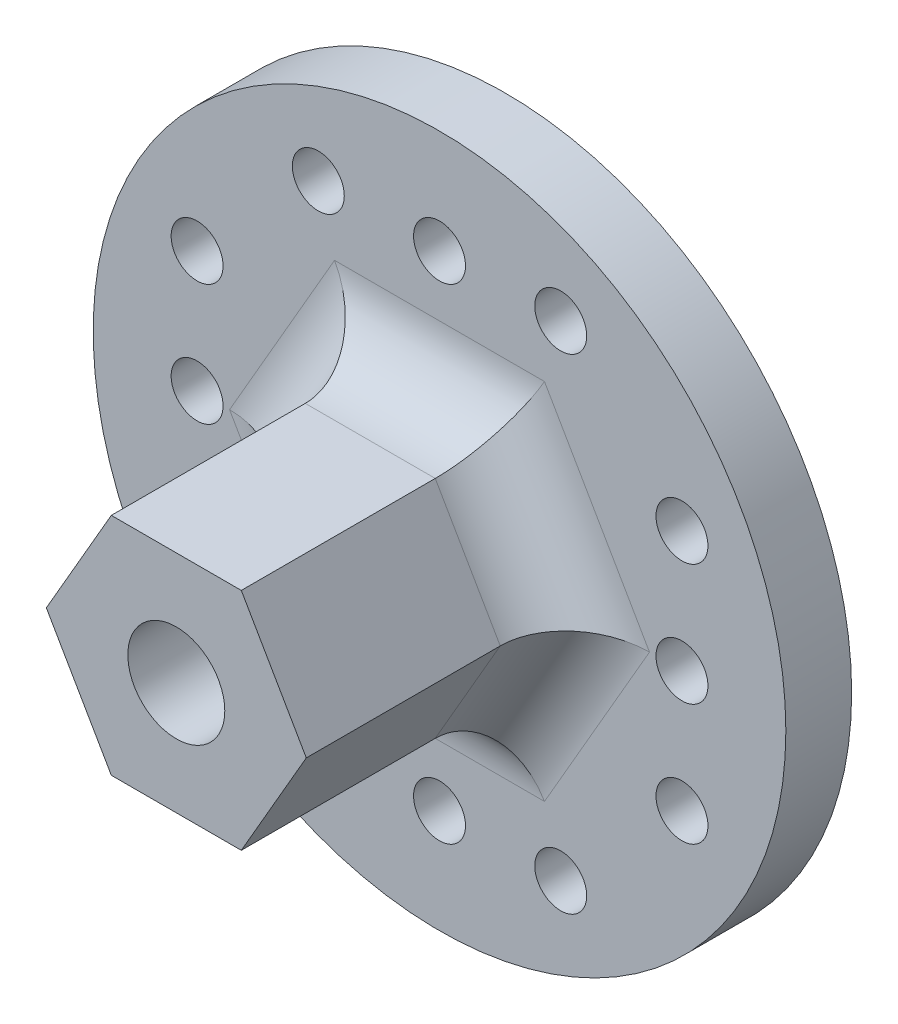
SolidWorks part; units mm, degrees
ref_plane "Front Plane" through (0, 0, 0) normal (0, 0, 1) x (1, 0, 0)
ref_plane "Top Plane" through (0, 0, 0) normal (0, 1, 0) x (1, 0, 0)
ref_plane "Right Plane" through (0, 0, 0) normal (1, 0, 0) x (0, 0, -1)
sketch "Sketch1" plane through (0, 0, 0) normal (0, 0, 1) x (1, 0, 0)
  line L0 (-7, 3.5) -> (-7, -3.5) construction
  line L1 (-7, 0) -> (0, 0) construction
  circle A0 centre (0, 0) radius 10
  circle A1 centre (-7, 0) radius 0.75
  circle A2 centre (3.5, 7) radius 0.75
  circle A3 centre (0, 7) radius 0.75
  circle A4 centre (-3.5, 7) radius 0.75
  circle A5 centre (7, -3.5) radius 0.75
  circle A6 centre (7, 0) radius 0.75
  circle A7 centre (7, 3.5) radius 0.75
  circle A8 centre (-3.5, -7) radius 0.75
  circle A9 centre (0, -7) radius 0.75
  circle A10 centre (3.5, -7) radius 0.75
  circle A11 centre (-7, -3.5) radius 0.75
  circle A12 centre (-7, 3.5) radius 0.75
  point P22 (0, 0)
  point P30 (0, 0)
  dimension "D1" = 7
  dimension "D2" = 7
  dimension "D3" = 0
  dimension "D7" = 1.5
  dimension "D4" = 0
  dimension "D5" = 0
  dimension "D6" = 0
  dimension "D8" = 3.5
  dimension "D9" = 1.5
  dimension "D10" = 1.5
  dimension "D11" = 20
  dimension "D13" = 7
  dimension "D14" = 7
  dimension "D12" = 4
extrude "Boss-Extrude1" add sketch "Sketch1" along normal blind 1.9
sketch "Sketch2" plane through (0, 0, 1.9) normal (0, 0, 1) x (1, 0, 0)
  line L0 (-10, 0) -> (10, 0) construction
  line L1 (0.7448, -9.9722) -> (0.7448, 9.9722) construction
  line L3 (3.7528, 0) -> (1.8764, 3.25)
  line L4 (1.8764, 3.25) -> (-1.8764, 3.25)
  line L5 (-1.8764, 3.25) -> (-3.7528, 0)
  line L6 (-3.7528, 0) -> (-1.8764, -3.25)
  line L7 (-1.8764, -3.25) -> (1.8764, -3.25)
  line L8 (1.8764, -3.25) -> (3.7528, 0)
  circle A0 centre (0, 0) radius 10 construction
  circle A1 centre (0, 0) radius 3.25 construction
  dimension "D1" = 6.5
extrude "Boss-Extrude2" add sketch "Sketch2" along normal blind 7.6
sketch "Sketch3" plane through (0, 0, 0) normal (0, 0, -1) x (-1, 0, 0)
  line L0 (-3.25, 0) -> (3.25, 0)
  arc A0 (-3.25, 0) -> (3.25, 0) centre (0, 0) ccw
  dimension "D1" = 6.5
sketch "Sketch4" plane through (0, 0, 9.5) normal (0, 0, 1) x (1, 0, 0)
  line L0 (2.8146, 1.625) -> (-2.8146, -1.625) construction
  line L1 (3.7528, 0) -> (1.8764, 3.25) construction
  line L2 (-3.7528, 0) -> (-1.8764, -3.25) construction
  line L3 (-1.8764, 3.25) -> (1.8764, -3.25) construction
  circle A0 centre (0, 0) radius 1.4
  dimension "D1" = 2.8
extrude "Cut-Extrude2" cut sketch "Sketch4" against normal blind 5
revolve "Cut-Revolve1" cut sketch "Sketch3" angle 360 about L0
fillet "Fillet1" radius 2 6 edges at (-2.8146, 1.625, 1.9) (-2.8146, -1.625, 1.9) (0, -3.25, 1.9) (2.8146, -1.625, 1.9) (2.8146, 1.625, 1.9) (0, 3.25, 1.9)
